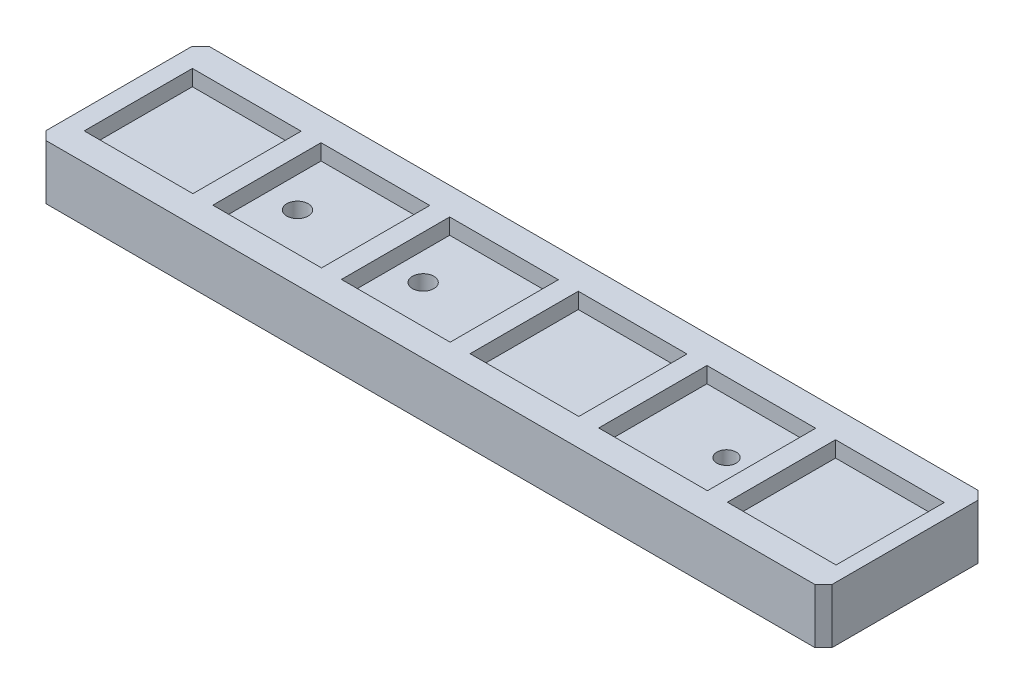
SolidWorks part; units mm, degrees
ref_plane "Plano frontal" through (0, 0, 0) normal (0, 0, 1) x (1, 0, 0)
ref_plane "Plano superior" through (0, 0, 0) normal (0, 1, 0) x (1, 0, 0)
ref_plane "Plano direito" through (0, 0, 0) normal (1, 0, 0) x (0, 0, -1)
sketch "Esboço1" plane through (0, 0, 0) normal (0, 1, 0) x (1, 0, 0)
  line L1 (0, 0) -> (-183.2, 0)
  line L2 (0, 0) -> (0, 38.02)
  line L3 (0, 38.02) -> (-183.2, 38.02)
  line L4 (-183.2, 0) -> (-183.2, 38.02)
  dimension "D1" = 183.2
  dimension "D2" = 38.02
extrude "Ressalto-extrusão1" add sketch "Esboço1" along normal blind 12.75
sketch "Esboço3" plane through (0, 12.75, 0) normal (0, 1, 0) x (1, 0, 0)
  line L0 (-183.2, 38.02) -> (-183.2, 0) construction
  line L2 (0, 38.02) -> (-183.2, 38.02) construction
  line L4 (-183.2, 0) -> (0, 0) construction
  line L8 (-178.7, 31.62) -> (-3.46, 31.62)
  line L9 (-3.46, 31.62) -> (-3.46, 6.4)
  line L10 (-3.46, 6.4) -> (-178.7, 6.4)
  line L11 (-178.7, 6.4) -> (-178.7, 31.62)
  line L17 (-153.36, 6.4) -> (-153.36, 31.62)
  line L18 (-148.72, 6.4) -> (-148.72, 31.62)
  line L19 (-123.38, 6.4) -> (-123.38, 31.62)
  line L20 (-118.74, 6.4) -> (-118.74, 31.62)
  line L21 (-93.4, 6.4) -> (-93.4, 31.62)
  line L22 (-88.76, 6.4) -> (-88.76, 31.62)
  line L23 (-63.42, 6.4) -> (-63.42, 31.62)
  line L24 (-58.78, 6.4) -> (-58.78, 31.62)
  line L25 (-33.44, 6.4) -> (-33.44, 31.62)
  line L26 (-28.8, 6.4) -> (-28.8, 31.62)
  dimension "D1" = 6.4
  dimension "D2" = 6.4
  dimension "D3" = 4.64
  dimension "D4" = 4.5
  dimension "D5" = 25.34
  dimension "D6" = 25.34
  dimension "D7" = 25.34
  dimension "D8" = 25.34
  dimension "D9" = 25.34
  dimension "D10" = 25.34
  dimension "D11" = 4.64
  dimension "D12" = 4.64
  dimension "D13" = 4.64
  dimension "D14" = 4.64
extrude "Corte-extrusão1" cut sketch "Esboço3" against normal blind 3.7 contours L10 L17 L8 L11 | L10 L19 L8 L18 | L10 L21 L8 L20 | L10 L23 L8 L22 | L10 L25 L8 L24 | L26 L10 L9 L8
chamfer "Chanfro1" distance 2 angle 45 4 edges at (-183.2, 6.375, 0) (0, 6.375, -38.02) (0, 6.375, 0) (-183.2, 6.375, -38.02)
sketch "Esboço4" plane through (0, 12.75, 0) normal (0, 1, 0) x (1, 0, 0)
  line L0 (-183.2, 36.02) -> (-183.2, 2) construction
  line L2 (0, 2) -> (0, 36.02) construction
  circle A0 centre (-41.6, 19.01) radius 2.25
  circle A1 centre (-141.6, 19.01) radius 2.5
  circle A2 centre (-112.3107, 19.01) radius 2.5
  point P6 (-183.2, 19.01)
  dimension "D1" = 100
  dimension "D2" = 70.7107
  dimension "D3" = 41.6
  dimension "D4" = 41.6
extrude "Corte-extrusão2" cut sketch "Esboço4" against normal blind 10100
